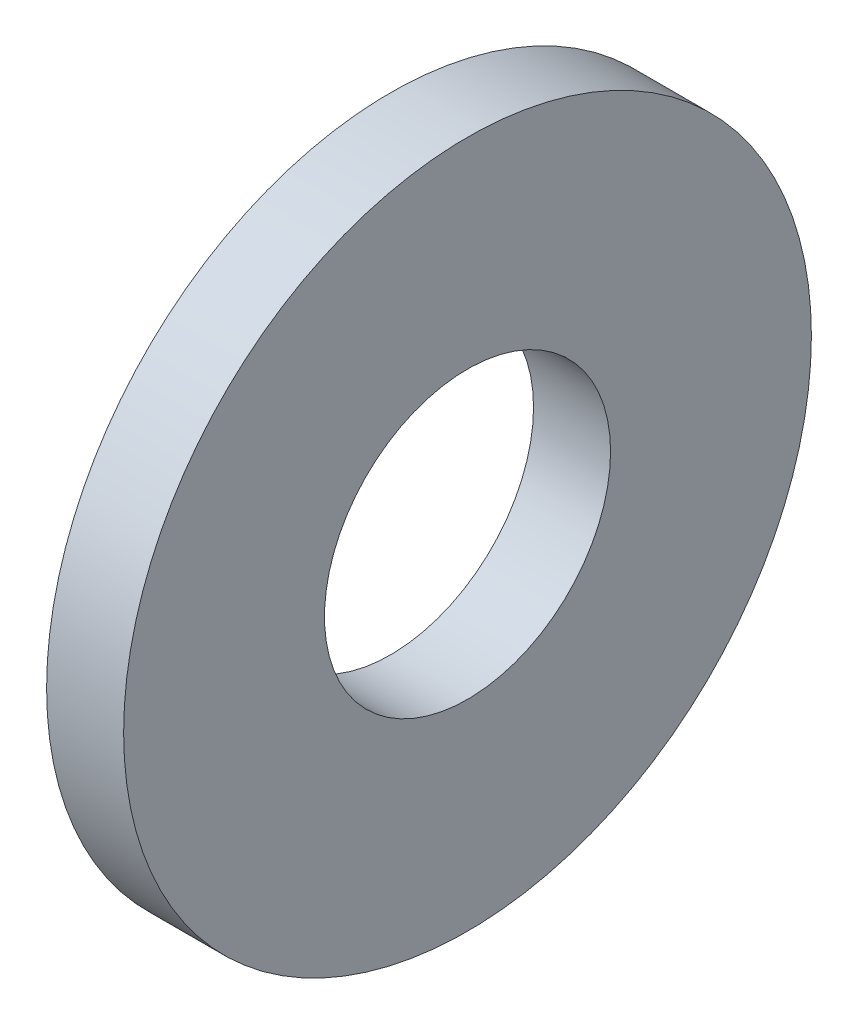
SolidWorks part; units mm, degrees
ref_plane "Front Plane" through (0, 0, 0) normal (0, 0, 1) x (1, 0, 0)
ref_plane "Top Plane" through (0, 0, 0) normal (0, 1, 0) x (1, 0, 0)
ref_plane "Right Plane" through (0, 0, 0) normal (1, 0, 0) x (0, 0, -1)
sketch "Sketch1" plane through (0, 0, 0) normal (1, 0, 0) x (0, 0, -1)
  circle A0 centre (0, 0) radius 7.9375
  circle A1 centre (0, 0) radius 3.302
  dimension "OD" = 15.875
  dimension "ID" = 6.604
extrude "Boss-Extrude1" add sketch "Sketch1" along normal blind 1.778
move or copy body "Body-Move/Copy1" [suppressed] bodies to move or copy 101
